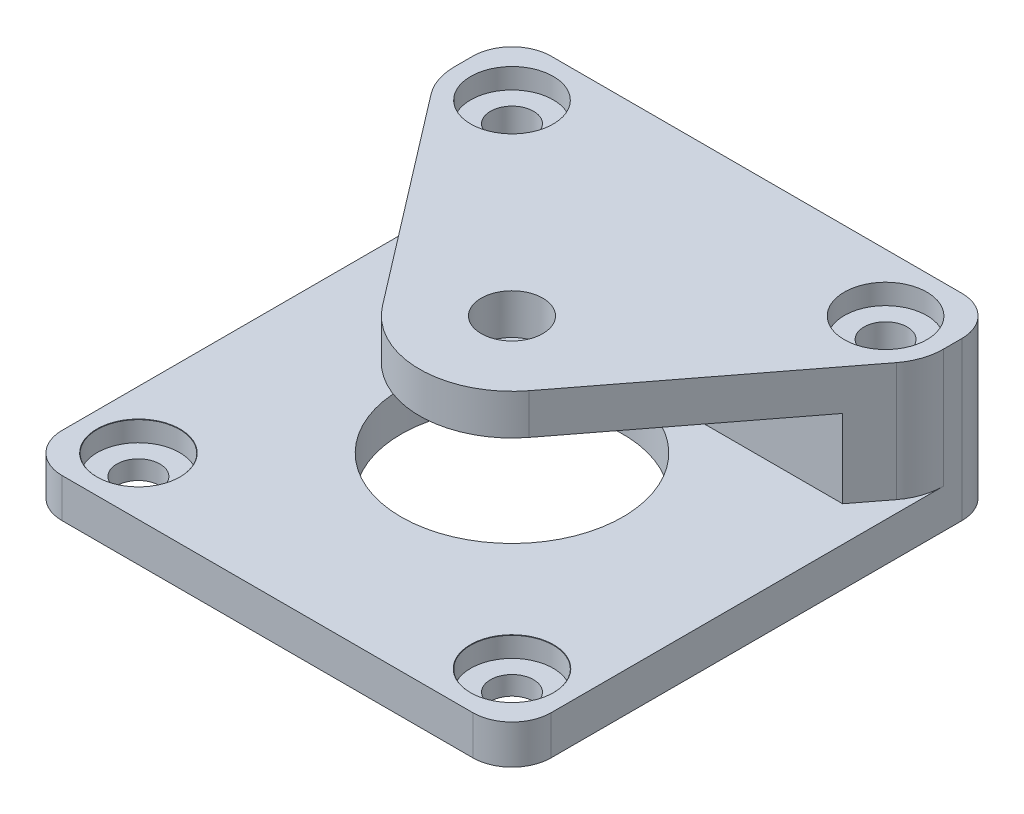
SolidWorks part; units mm, degrees
ref_plane "Front Plane" through (0, 0, 0) normal (0, 0, 1) x (1, 0, 0)
ref_plane "Top Plane" through (0, 0, 0) normal (0, 1, 0) x (1, 0, 0)
ref_plane "Right Plane" through (0, 0, 0) normal (1, 0, 0) x (0, 0, -1)
sketch "Sketch1" plane through (0, 0, 0) normal (0, 1, 0) x (1, 0, 0)
  line L1 (0, 0) -> (39.69, 0)
  line L2 (0, 0) -> (0, 39.69)
  line L3 (0, 39.69) -> (39.69, 39.69)
  line L4 (39.69, 0) -> (39.69, 39.69)
  line L5 (0, 0) -> (39.69, 39.69) construction
  line L6 (0, 39.69) -> (39.69, 0) construction
  circle A0 centre (4.685, 4.685) radius 1.75
  circle A1 centre (35.005, 4.685) radius 1.75
  circle A2 centre (35.005, 35.005) radius 1.75
  circle A3 centre (4.685, 35.005) radius 1.75
  circle A4 centre (19.845, 19.845) radius 9
  point P4 (19.845, 19.845)
  dimension "D4" = 3.5
  dimension "D5" = 18
  dimension "D1" = 39.69
  dimension "D2" = 39.69
  dimension "D3" = 15.16
extrude "Boss-Extrude1" add sketch "Sketch1" along normal blind 3.175
sketch "Sketch2" plane through (0, 3.175, 0) normal (0, 1, 0) x (1, 0, 0)
  line L0 (19.845, 0) -> (19.845, 39.69) construction
  line L1 (0, 0) -> (39.69, 0) construction
  line L2 (39.69, 39.69) -> (0, 39.69) construction
  line L3 (0, 19.845) -> (39.69, 19.845) construction
  line L4 (0, 39.69) -> (0, 0) construction
  line L5 (39.69, 0) -> (39.69, 39.69) construction
  line L6 (0, 35.005) -> (0, 39.69)
  line L7 (0, 39.69) -> (4.685, 39.69)
  line L8 (4.685, 39.69) -> (35.005, 39.69)
  line L9 (35.005, 39.69) -> (39.69, 39.69)
  line L10 (39.69, 39.69) -> (39.69, 35.005)
  line L11 (25.7987, 15.2839) -> (38.7241, 32.1559)
  line L12 (13.8913, 15.2839) -> (0.9659, 32.1559)
  arc A0 (13.8913, 15.2839) -> (25.7987, 15.2839) centre (19.845, 19.845) ccw
  circle A1 centre (35.005, 35.005) radius 1.75 construction
  circle A2 centre (4.685, 35.005) radius 1.75 construction
  circle A3 centre (35.005, 35.005) radius 1.75
  circle A4 centre (4.685, 35.005) radius 1.75
  arc A5 (0, 35.005) -> (0.9659, 32.1559) centre (4.685, 35.005) ccw
  arc A6 (38.7241, 32.1559) -> (39.69, 35.005) centre (35.005, 35.005) ccw
  dimension "D1" = 15
extrude "Boss-Extrude2" add sketch "Sketch2" along normal blind 9.635
sketch "Sketch3" plane through (0, 0, 0) normal (-1, 0, 0) x (0, 0, 1)
  line L0 (0, 3.175) -> (0, 0) construction
  line L1 (-29.69, 3.175) -> (0, 3.175)
  line L2 (-29.69, 3.175) -> (-29.69, 9.525)
  line L3 (-29.69, 9.525) -> (0, 9.525)
  line L4 (0, 3.175) -> (0, 9.525)
  line L5 (-29.69, 3.175) -> (0, 9.525) construction
  line L6 (-29.69, 9.525) -> (0, 3.175) construction
  line L7 (-35.005, 3.175) -> (0, 3.175) construction
  line L8 (-39.69, 12.81) -> (-39.69, 0) construction
  point P4 (-14.845, 6.35)
  dimension "D1" = 6.35
  dimension "D2" = 10
extrude "Cut-Extrude1" cut sketch "Sketch3" against normal through all contours L3 L4 L1 L2
hole_wizard "CBORE for M3 SBHCS1" positions "Sketch4" profile "Sketch5" counterbore size "M3" standard "ANSI Metric"
sketch "Sketch4" plane through (0, 12.81, 0) normal (0, 1, 0) x (1, 0, 0)
  point P0 (4.685, 35.005)
  point P3 (35.005, 35.005)
sketch "Sketch5" plane through (4.685, 12.81, -35.005) normal (1, 0, 0) x (0, 0, 1)
  line L0 (0, 0) -> (0, 15.3215)
  line L1 (0, 15.3215) -> (1.7, 14.3)
  line L2 (1.7, 14.3) -> (1.7, 1.65)
  line L3 (1.7, 1.65) -> (3.35, 1.65)
  line L4 (3.35, 1.65) -> (3.35, 0)
  line L5 (3.35, 0) -> (0, 0)
  line L10 (0, 15.3215) -> (-1.7, 14.3) construction
  line L11 (0, -6.35) -> (0, 107.95) construction
  dimension "Hole Dia." = 3.4
  dimension "Hole Depth" = 14.3
  dimension "C'Bore Dia." = 6.7
  dimension "C'Bore Depth" = 1.65
  dimension "Drill Angle" = 118
hole_wizard "CBORE for M3 SBHCS2" positions "Sketch6" profile "Sketch7" counterbore size "M3" standard "ANSI Metric"
sketch "Sketch6" plane through (0, 3.175, 0) normal (0, 1, 0) x (1, 0, 0)
  point P0 (4.685, 4.685)
  point P3 (35.005, 4.685)
sketch "Sketch7" plane through (4.685, 3.175, -4.685) normal (1, 0, 0) x (0, 0, 1)
  line L0 (0, 0) -> (0, 15.3215)
  line L1 (0, 15.3215) -> (1.7, 14.3)
  line L2 (1.7, 14.3) -> (1.7, 1.65)
  line L3 (1.7, 1.65) -> (3.35, 1.65)
  line L5 (3.35, 1.65) -> (3.35, 0.025)
  line L6 (3.35, 0.025) -> (3.375, 0)
  line L7 (3.375, 0) -> (0, 0)
  line L8 (-3.35, 0.025) -> (-3.375, 0) construction
  line L10 (0, 15.3215) -> (-1.7, 14.3) construction
  line L11 (0, -6.35) -> (0, 107.95) construction
  dimension "Hole Dia." = 3.4
  dimension "Hole Depth" = 14.3
  dimension "C'Bore Dia." = 6.7
  dimension "C'Bore Depth" = 1.65
  dimension "Near C'Sink Dia." = 6.75
  dimension "Near C'Sink Angle" = 90
  dimension "Drill Angle" = 118
fillet "Fillet1" radius 3.175 4 edges at (0, 6.405, -39.69) (39.69, 6.405, -39.69) (39.69, 1.5875, 0) (0, 1.5875, 0)
sketch "Sketch8" plane through (0, 12.81, 0) normal (0, 1, 0) x (1, 0, 0)
  arc A0 (13.8913, 15.2839) -> (25.7987, 15.2839) centre (19.845, 19.845) ccw construction
  arc A1 (13.8913, 15.2839) -> (25.7987, 15.2839) centre (19.845, 19.845) ccw
  circle A2 centre (19.845, 19.845) radius 2.5
  dimension "D1" = 5
extrude "Cut-Extrude2" cut sketch "Sketch8" against normal up to next contours A2
